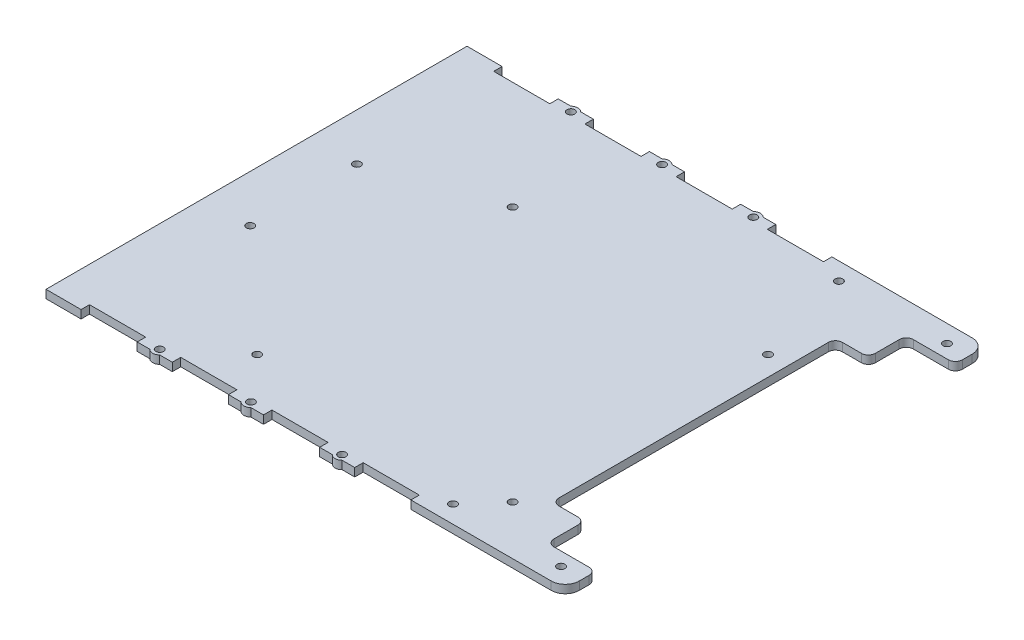
SolidWorks part; units mm, degrees
ref_plane "Front Plane" through (0, 0, 0) normal (0, 0, 1) x (1, 0, 0)
ref_plane "Top Plane" through (0, 0, 0) normal (0, 1, 0) x (1, 0, 0)
ref_plane "Right Plane" through (0, 0, 0) normal (1, 0, 0) x (0, 0, -1)
sketch "Sketch2" plane through (0, 0, 0) normal (0, 1, 0) x (1, 0, 0)
  line L0 (-69.0048, 0) -> (90.0153, 0) construction
  line L1 (-69.0048, -76.2) -> (-69.0048, 76.2)
  line L2 (-69.0048, 76.2) -> (118.9552, 76.2)
  line L3 (118.9552, 76.2) -> (118.9552, -76.2)
  line L4 (-69.0048, -76.2) -> (118.9552, -76.2)
  point P7 (118.9552, 0)
  point P8 (0, 0)
  dimension "D1" = 76.2
  dimension "D2" = 187.96
extrude "Boss-Extrude1" add sketch "Sketch2" along normal blind 2.9718
sketch "Sketch4" plane through (0, 2.9718, 0) normal (0, 1, 0) x (1, 0, 0)
  line L0 (-56.3048, -82.7094) -> (-56.3048, -73.152)
  line L1 (-56.3048, -73.152) -> (-35.9848, -73.152)
  line L2 (-35.9848, -73.152) -> (-35.9848, -90.0859)
  line L3 (-69.0048, 76.2) -> (-69.0048, -76.2) construction
  line L4 (-69.0048, -76.2) -> (118.9552, -76.2) construction
  line L5 (-23.2848, -82.7094) -> (-23.2848, -73.152)
  line L6 (-23.2848, -73.152) -> (-2.9648, -73.152)
  line L7 (-2.9648, -73.152) -> (-2.9648, -90.0859)
  line L8 (9.7352, -82.7094) -> (9.7352, -73.152)
  line L9 (9.7352, -73.152) -> (30.0552, -73.152)
  line L10 (30.0552, -73.152) -> (30.0552, -90.0859)
  line L11 (42.7552, -82.7094) -> (42.7552, -73.152)
  line L12 (42.7552, -73.152) -> (63.0752, -73.152)
  line L13 (63.0752, -73.152) -> (63.0752, -90.0859)
  line L14 (-1.6345, 0) -> (1.6345, 0) construction
  line L15 (63.0752, 73.152) -> (63.0752, 90.0859)
  line L16 (42.7552, 73.152) -> (63.0752, 73.152)
  line L17 (42.7552, 82.7094) -> (42.7552, 73.152)
  line L18 (30.0552, 73.152) -> (30.0552, 90.0859)
  line L19 (9.7352, 73.152) -> (30.0552, 73.152)
  line L20 (9.7352, 82.7094) -> (9.7352, 73.152)
  line L21 (-2.9648, 73.152) -> (-2.9648, 90.0859)
  line L22 (-23.2848, 73.152) -> (-2.9648, 73.152)
  line L23 (-23.2848, 82.7094) -> (-23.2848, 73.152)
  line L24 (-35.9848, 73.152) -> (-35.9848, 90.0859)
  line L25 (-56.3048, 73.152) -> (-35.9848, 73.152)
  line L26 (-56.3048, 82.7094) -> (-56.3048, 73.152)
  line L27 (118.9552, -76.2) -> (118.9552, 76.2) construction
  line L28 (0, 0) -> (144.6724, 0) construction
  line L29 (30.6739, 76.2) -> (41.5595, 76.2)
  line L30 (118.9552, 76.2) -> (-69.0048, 76.2) construction
  line L31 (34.283, 76.2) -> (38.5273, 76.2)
  line L32 (34.283, 76.2) -> (38.5273, 76.2)
  line L33 (34.283, 76.2) -> (38.5273, 76.2)
  circle A5 centre (82.1252, -58.42) radius 1.397
  circle A7 centre (-10.3308, -58.42) radius 1.397
  circle A8 centre (36.4052, 74.422) radius 1.397
  arc A9 (38.5273, 76.2) -> (34.283, 76.2) centre (36.4052, 74.422) ccw
  circle A10 centre (3.3852, 74.422) radius 1.397
  arc A11 (5.5073, 76.2) -> (1.263, 76.2) centre (3.3852, 74.422) ccw
  circle A12 centre (-29.6348, 74.422) radius 1.397
  arc A13 (-27.5127, 76.2) -> (-31.757, 76.2) centre (-29.6348, 74.422) ccw
  circle A14 centre (36.4052, -74.422) radius 1.397
  arc A15 (38.5273, -76.2) -> (34.283, -76.2) centre (36.4052, -74.422) cw
  circle A16 centre (3.3852, -74.422) radius 1.397
  arc A17 (5.5073, -76.2) -> (1.263, -76.2) centre (3.3852, -74.422) cw
  circle A18 centre (-29.6348, -74.422) radius 1.397
  arc A19 (-27.5127, -76.2) -> (-31.757, -76.2) centre (-29.6348, -74.422) cw
  circle A20 centre (111.0813, 69.85) radius 1.397
  circle A21 centre (111.0813, -69.85) radius 1.397
  circle A22 centre (71.9653, 69.85) radius 1.397
  circle A23 centre (71.9653, -69.85) radius 1.397
  circle A24 centre (82.1252, 34.036) radius 1.397
  circle A25 centre (-10.3308, 34.036) radius 1.397
  dimension "D5" = 92.456
  dimension "D6" = 2
  dimension "D9" = 39.116
  dimension "D11" = 92.456
  dimension "D12" = 1.778
  dimension "D15" = 2
  dimension "D7" = 17.78
  dimension "D8" = 36.83
  dimension "D1" = 12.7
  dimension "D2" = 20.32
  dimension "D3" = 3.048
  dimension "D13" = 6.35
  dimension "D4" = 4
  dimension "D10" = 2
  dimension "D14" = 3
extrude "Cut-Extrude1" cut sketch "Sketch4" against normal blind 5.08
sketch "Sketch5" plane through (0, 2.9718, 0) normal (0, 1, 0) x (1, 0, 0)
  line L0 (30.0552, 76.2) -> (42.7552, 76.2)
  line L1 (34.6253, 76.2) -> (38.185, 76.2)
  line L3 (-1.6345, 0) -> (1.6345, 0) construction
  arc A0 (38.185, 76.2) -> (34.6253, 76.2) centre (36.4052, 74.422) ccw
  arc A1 (5.165, 76.2) -> (1.6053, 76.2) centre (3.3852, 74.422) ccw
  arc A2 (-27.855, 76.2) -> (-31.4147, 76.2) centre (-29.6348, 74.422) ccw
  arc A3 (-27.855, -76.2) -> (-31.4147, -76.2) centre (-29.6348, -74.422) cw
  arc A4 (5.165, -76.2) -> (1.6053, -76.2) centre (3.3852, -74.422) cw
  arc A5 (38.185, -76.2) -> (34.6253, -76.2) centre (36.4052, -74.422) cw
  line M14 (-35.9848, -76.2) -> (-23.2848, -76.2)
  line M18 (-2.9648, -76.2) -> (9.7352, -76.2)
  line M22 (30.0552, -76.2) -> (42.7552, -76.2)
  line M36 (9.7352, 76.2) -> (-2.9648, 76.2)
  line M40 (-23.2848, 76.2) -> (-35.9848, 76.2)
  dimension "D1" = 3
extrude "Boss-Extrude2" add sketch "Sketch5" against normal blind 2.9718 contours L0 A0 | A1 M36 | A2 M40 | A3 M14 | A4 M18 | A5 M22
fillet "Fillet1" radius 5.08 2 edges at (118.9552, 1.4859, 76.2) (118.9552, 1.4859, -76.2)
sketch "Sketch6" plane through (0, 2.9718, 0) normal (0, 1, 0) x (1, 0, 0)
  line L0 (-81.8181, 0) -> (160.7986, 0) construction
  line L1 (118.9552, -98.38) -> (118.9552, -65.024)
  line L2 (118.9552, -71.12) -> (118.9552, 71.12) construction
  line L3 (118.9552, -65.024) -> (101.1752, -65.024)
  line L4 (101.1752, -65.024) -> (101.1752, -51.308)
  line L5 (101.1752, -51.308) -> (89.2372, -51.308)
  line L6 (89.2372, -51.308) -> (89.2372, 51.308)
  line L7 (63.0752, -76.2) -> (113.8752, -76.2) construction
  line L8 (118.9552, -98.38) -> (174.7614, -98.38)
  line L9 (118.9552, 98.38) -> (174.7614, 98.38)
  line L10 (118.9552, 98.38) -> (118.9552, 65.024)
  line L11 (118.9552, 65.024) -> (101.1752, 65.024)
  line L12 (101.1752, 65.024) -> (101.1752, 51.308)
  line L13 (101.1752, 51.308) -> (89.2372, 51.308)
  line L14 (174.7614, 98.38) -> (174.7614, -98.38)
  point P20 (89.2372, 0)
  dimension "D1" = 11.176
  dimension "D2" = 17.78
  dimension "D3" = 13.716
  dimension "D4" = 11.938
  dimension "D5" = 51.308
extrude "Cut-Extrude2" cut sketch "Sketch6" against normal blind 5.08
fillet "Fillet2" radius 2.54 1 edges at (101.1752, 1.4859, -51.308)
fillet "Fillet3" radius 2.54 5 edges at (118.9552, 1.4859, 65.024) (101.1752, 1.4859, 65.024) (101.1752, 1.4859, 51.308) (118.9552, 1.4859, -65.024) (101.1752, 1.4859, -65.024)
sketch "Sketch7" plane through (0, 2.9718, 0) normal (0, 1, 0) x (1, 0, 0)
  line L0 (-98.6382, 0) -> (148.4409, 0) construction
  line L1 (-69.0048, 76.2) -> (-69.0048, -76.2) construction
  circle A0 centre (-51.9868, 19.304) radius 1.397
  circle A1 centre (-51.9868, -19.304) radius 1.397
  dimension "D1" = 2.794
  dimension "D2" = 19.304
  dimension "D3" = 17.018
extrude "Cut-Extrude3" cut sketch "Sketch7" against normal blind 5.08
fillet "Fillet5" radius 2.54 1 edges at (89.2372, 1.4859, -51.308)
fillet "Fillet6" radius 2.54 1 edges at (89.2372, 1.4859, 51.308)
